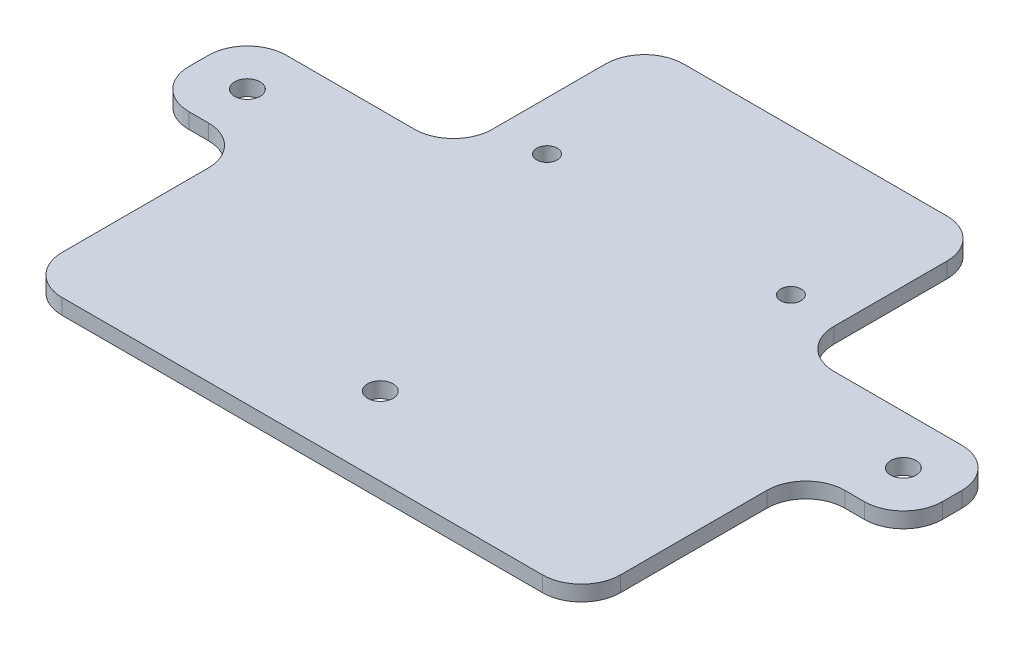
SolidWorks part; units mm, degrees
material "6061-T6 (SS)"
ref_plane "Front Plane" through (0, 0, 0) normal (0, 0, 1) x (1, 0, 0)
ref_plane "Top Plane" through (0, 0, 0) normal (0, 1, 0) x (1, 0, 0)
ref_plane "Right Plane" through (0, 0, 0) normal (1, 0, 0) x (0, 0, -1)
sketch "Sketch1" plane through (0, 0, 0) normal (0, 1, 0) x (1, 0, 0)
  line L0 (0, 0) -> (0, -107.5) construction
  line L1 (-57.25, -107.5) -> (57.25, -107.5) construction
  line L2 (-57.25, -107.5) -> (-57.25, 107.5) construction
  line L3 (-57.25, 107.5) -> (57.25, 107.5) construction
  line L4 (57.25, -107.5) -> (57.25, 107.5) construction
  line L5 (-57.25, -107.5) -> (57.25, 107.5) construction
  line L6 (-57.25, 107.5) -> (57.25, -107.5) construction
  line L7 (-25, -75) -> (25, -75) construction
  line L8 (-57.25, -81) -> (57.25, -81) construction
  line L9 (-57.25, -84.175) -> (57.25, -84.175) construction
  line L10 (-57.25, -144.175) -> (57.25, -144.175) construction
  line L11 (-57.25, -94.175) -> (57.25, -94.175) construction
  line L12 (-57.25, -114.175) -> (57.25, -114.175) construction
  line L13 (-57.25, -134.175) -> (57.25, -134.175) construction
  point P0 (0, 0)
  point P10 (0, -75)
  dimension "D1" = 114.5
  dimension "D2" = 215
  dimension "D3" = 50
  dimension "D4" = 32.5
  dimension "D5" = 6
  dimension "D6" = 3.175
  dimension "D7" = 60
  dimension "D8" = 10
  dimension "D9" = 20
  dimension "D10" = 20
sketch "Sketch3" plane through (0, 0, 0) normal (0, 1, 0) x (1, 0, 0)
  line L0 (-35, -45) -> (35, -45)
  line L1 (35, -45) -> (35, -84.175)
  line L2 (-57.25, -84.175) -> (57.25, -84.175) construction
  line L3 (35, -84.175) -> (77.25, -84.175)
  line L4 (77.25, -84.175) -> (77.25, -104.175)
  line L5 (77.25, -104.175) -> (57.25, -104.175)
  line L6 (57.25, -107.5) -> (57.25, 107.5) construction
  line L7 (57.25, -104.175) -> (57.25, -150.175)
  line L8 (-57.25, -144.175) -> (57.25, -144.175) construction
  line L9 (-57.25, -150.175) -> (57.25, -150.175)
  line L10 (0, 0) -> (0, -107.5) construction
  line L11 (-25, -75) -> (25, -75) construction
  line L12 (0, -45) -> (0, -144.175) construction
  line L13 (-57.25, -104.175) -> (-57.25, -150.175)
  line L14 (-77.25, -104.175) -> (-57.25, -104.175)
  line L15 (-77.25, -84.175) -> (-77.25, -104.175)
  line L16 (-35, -84.175) -> (-77.25, -84.175)
  line L17 (-35, -45) -> (-35, -84.175)
  line L18 (77.25, -94.175) -> (-77.25, -94.175) construction
  line L19 (-57.25, -134.175) -> (57.25, -134.175) construction
  circle A0 centre (-25, -75) radius 2.1
  circle A1 centre (25, -75) radius 2.1
  circle A2 centre (-67.25, -94.175) radius 2.6
  circle A3 centre (67.25, -94.175) radius 2.6
  circle A4 centre (0, -134.175) radius 2.6
  dimension "D5" = 4.2
  dimension "D7" = 5.2
  dimension "D1" = 30
  dimension "D2" = 10
  dimension "D3" = 20
  dimension "D4" = 20
  dimension "D6" = 10
  dimension "D8" = 6
extrude "Boss-Extrude1" add sketch "Sketch3" along normal blind 3.175
fillet "Fillet1" radius 8 12 edges at (-35, 1.5875, 84.175) (-77.25, 1.5875, 84.175) (-77.25, 1.5875, 104.175) (-57.25, 1.5875, 104.175) (-57.25, 1.5875, 150.175) (57.25, 1.5875, 150.175) (57.25, 1.5875, 104.175) (77.25, 1.5875, 104.175) (77.25, 1.5875, 84.175) (35, 1.5875, 84.175) (-35, 1.5875, 45) (35, 1.5875, 45)
